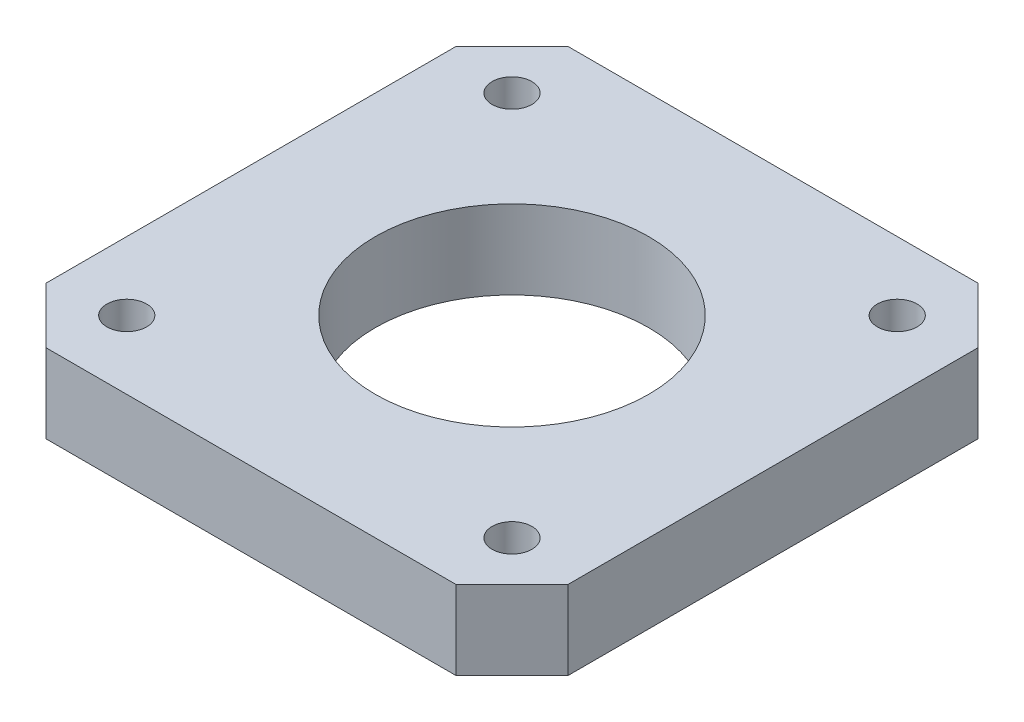
SolidWorks part; units mm, degrees
ref_plane "Front Plane" through (0, 0, 0) normal (0, 0, 1) x (1, 0, 0)
ref_plane "Top Plane" through (0, 0, 0) normal (0, 1, 0) x (1, 0, 0)
ref_plane "Right Plane" through (0, 0, 0) normal (1, 0, 0) x (0, 0, -1)
sketch "Sketch1" plane through (0, 0, 0) normal (0, 1, 0) x (1, 0, 0)
  line L0 (-21, -21) -> (-21, 21)
  line L1 (-21, -21) -> (21, -21)
  line L2 (-21, 21) -> (21, 21)
  line L3 (21, -21) -> (21, 21)
  line L4 (-21, -21) -> (21, 21) construction
  line L5 (-21, 21) -> (21, -21) construction
  point P1 (0, 0)
  dimension "D1" = 42
  dimension "D2" = 42
extrude "Boss-Extrude1" add sketch "Sketch1" along normal blind 6.35
chamfer "Chamfer1" distance 4.5 angle 45 4 edges at (21, 3.175, 21) (-21, 3.175, 21) (21, 3.175, -21) (-21, 3.175, -21)
sketch "Sketch2" plane through (0, 6.35, 0) normal (0, 1, 0) x (1, 0, 0)
  line L0 (15.5, -15.5) -> (15.5, 15.5) construction
  line L1 (15.5, -15.5) -> (-15.5, -15.5) construction
  line L2 (15.5, 15.5) -> (-15.5, 15.5) construction
  line L3 (-15.5, -15.5) -> (-15.5, 15.5) construction
  line L4 (15.5, -15.5) -> (-15.5, 15.5) construction
  line L5 (15.5, 15.5) -> (-15.5, -15.5) construction
  point P1 (0, 0)
  dimension "D1" = 31
  dimension "D2" = 31
hole_wizard "M3 Clearance Hole1" positions "Sketch5" profile "Sketch4" hole size "M3" standard "ANSI Metric" end condition through all
sketch "Sketch5" plane through (0, 6.35, 0) normal (0, 1, 0) x (1, 0, 0)
  point P0 (-15.5, 15.5)
  point P3 (-15.5, -15.5)
  point P6 (15.5, -15.5)
  point P9 (15.5, 15.5)
sketch "Sketch4" plane through (-15.5, 6.35, -15.5) normal (1, 0, 0) x (0, 0, 1)
  line L0 (0, 0) -> (0, 6.35)
  line L1 (0, 6.35) -> (1.6, 6.35)
  line L2 (1.6, 6.35) -> (1.6, 0)
  line L5 (1.6, 0) -> (0, 0)
  line L11 (0, -6.35) -> (0, 107.95) construction
  dimension "Thru Hole Dia." = 3.2
  dimension "Thru Hole Depth" = 6.35
sketch "Sketch6" plane through (0, 6.35, 0) normal (0, 1, 0) x (1, 0, 0)
  circle A0 centre (0, 0) radius 11
  dimension "D1" = 22
extrude "Cut-Extrude1" cut sketch "Sketch6" against normal through all
